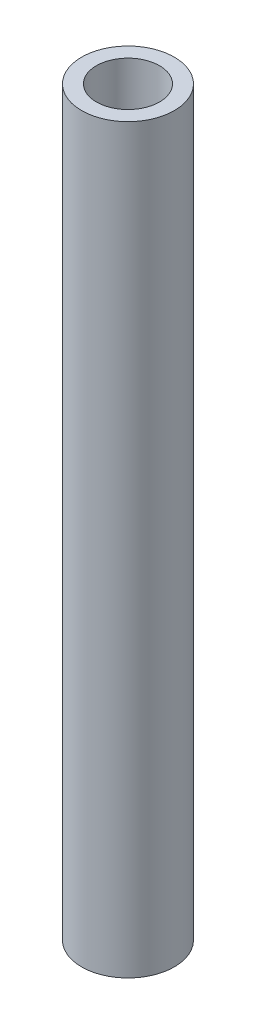
SolidWorks part; units mm, degrees
material "PTFE (general)"
ref_plane "Front Plane" through (0, 0, 0) normal (0, 0, 1) x (1, 0, 0)
ref_plane "Top Plane" through (0, 0, 0) normal (0, 1, 0) x (1, 0, 0)
ref_plane "Right Plane" through (0, 0, 0) normal (1, 0, 0) x (0, 0, -1)
sketch "Sketch1" plane through (0, 0, 0) normal (0, 1, 0) x (1, 0, 0)
  circle A0 centre (0, 0) radius 0.2125
  circle A1 centre (0, 0) radius 0.3125
  dimension "D1" = 0.1
  dimension "D2" = 0.425
extrude "Boss-Extrude1" add sketch "Sketch1" along normal blind 5
